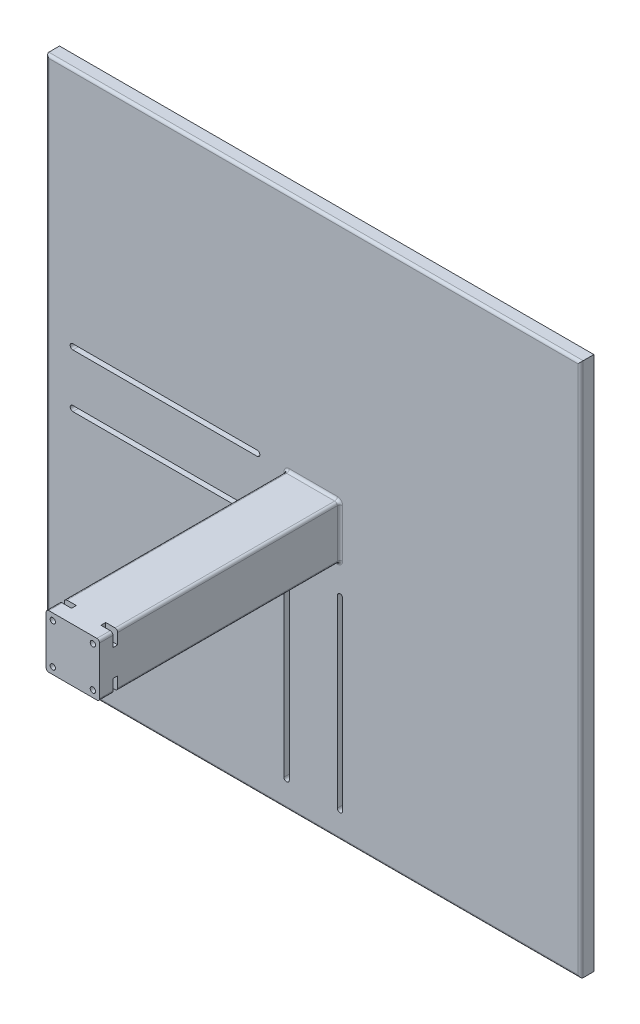
SolidWorks part; units mm, degrees
ref_plane "Plan de face" through (0, 0, 0) normal (0, 0, 1) x (1, 0, 0)
ref_plane "Plan de dessus" through (0, 0, 0) normal (0, 1, 0) x (1, 0, 0)
ref_plane "Plan de droite" through (0, 0, 0) normal (1, 0, 0) x (0, 0, -1)
sketch "Esquisse1" plane through (0, 0, 0) normal (0, 0, 1) x (1, 0, 0)
  line L1 (-100, 100) -> (100, 100)
  line L2 (-100, 100) -> (-100, -100)
  line L3 (-100, -100) -> (100, -100)
  line L4 (100, 100) -> (100, -100)
  dimension "D1" = 100
  dimension "D2" = 200
  dimension "D3" = 100
  dimension "D4" = 200
extrude "Boss.-Extru.1" add sketch "Esquisse1" along normal blind 5
sketch "Esquisse2" plane through (0, 0, 5) normal (0, 0, 1) x (1, 0, 0)
  line L0 (-100, 100) -> (-100, -100) construction
  line L1 (-15, -25) -> (15, -25)
  line L2 (-15, -25) -> (-15, -29)
  line L3 (-15, -29) -> (15, -29)
  line L4 (15, -25) -> (15, -29)
  line L5 (-25, 15) -> (-29, 15)
  line L6 (-25, 15) -> (-25, -15)
  line L7 (-25, -15) -> (-29, -15)
  line L8 (-29, 15) -> (-29, -15)
  line L9 (-100, -100) -> (100, -100) construction
  line L11 (100, -100) -> (100, 100) construction
  line L12 (100, 100) -> (-100, 100) construction
  point P12 (-25, 0)
  dimension "D1" = 75
  dimension "D2" = 75
  dimension "D3" = 30
  dimension "D4" = 30
  dimension "D5" = 85
  dimension "D6" = 85
  dimension "D7" = 85
  dimension "D8" = 85
  dimension "D9" = 4
  dimension "D10" = 4
extrude "Boss.-Extru.2" [suppressed] add sketch "Esquisse2" along normal blind 25
sketch "Esquisse3" [suppressed] plane through (0, 0, 5) normal (0, 0, 1) x (1, 0, 0)
  line L0 (-100, 100) -> (-100, -100) construction
  line L1 (-29, 20) -> (-100, 20)
  line L2 (-29, 20) -> (-29, -20)
  line L3 (-29, -20) -> (-100, -20)
  line L4 (-100, 20) -> (-100, -20)
  line L5 (-100, -100) -> (100, -100) construction
  line L6 (20, -100) -> (-20, -100)
  line L7 (20, -100) -> (20, -29)
  line L8 (20, -29) -> (-20, -29)
  line L9 (-20, -100) -> (-20, -29)
  line L10 (-15, -29) -> (15, -29) construction
  line L11 (-29, 15) -> (-29, -15) construction
  line L14 (-29, 15) -> (-29, -15) construction
  point P12 (0, -29)
  point P13 (-29, 0)
  dimension "D1" = 40
  dimension "D2" = 40
  dimension "D3" = 20
  dimension "D4" = 20
extrude "Boss.-Extru.3" [suppressed] add sketch "Esquisse3" along normal blind 5
fillet "Congé1" radius 1 4 edges at (0, -100, 5) (-100, 0, 5) (0, 100, 5) (100, 0, 5)
fillet "Congé2" [suppressed] radius 1
sketch "Esquisse4" plane through (0, 0, 5) normal (0, 0, 1) x (1, 0, 0)
  line L1 (-10, 10) -> (10, 10)
  line L2 (-10, 10) -> (-10, -10)
  line L3 (-10, -10) -> (10, -10)
  line L4 (10, 10) -> (10, -10)
  point P4 (0, 0)
  dimension "D1" = 10
  dimension "D2" = 20
  dimension "D3" = 10
  dimension "D4" = 20
extrude "Boss.-Extru.4" add sketch "Esquisse4" along normal blind 90
fillet "Congé3" radius 1 8 edges at (-10, 0, 5) (0, 10, 5) (0, -10, 5) (-10, 10, 50) (10, 10, 50) (10, 0, 5) (-10, -10, 50) (10, -10, 50)
sketch "Esquisse5" plane through (0, 0, 95) normal (0, 0, 1) x (1, 0, 0)
  line L0 (9, 10) -> (-9, 10) construction
  line L1 (-10, 9) -> (-10, -9) construction
  line L2 (10, -9) -> (10, 9) construction
  line L3 (-9, -10) -> (9, -10) construction
  circle A0 centre (7.5, 7.5) radius 1
  circle A1 centre (-7.5, 7.5) radius 1
  circle A2 centre (-7.5, -7.5) radius 1
  circle A3 centre (7.5, -7.5) radius 1
  dimension "D1" = 2
  dimension "D2" = 2.5
  dimension "D3" = 2.5
  dimension "D4" = 2.5
  dimension "D5" = 2.5
extrude "Enlèv. mat.-Extru.1" cut sketch "Esquisse5" against normal blind 5
sketch "Esquisse6" plane through (0, -10, 0) normal (0, -1, 0) x (1, 0, 0)
  line L0 (-9, 95) -> (9, 95) construction
  line L1 (-10, 90) -> (-5.5, 90)
  line L2 (-10, 90) -> (-10, 88.2)
  line L3 (-10, 88.2) -> (-5.5, 88.2)
  line L4 (-5.5, 90) -> (-5.5, 88.2)
  line L5 (10, 90) -> (5.5, 90)
  line L6 (10, 90) -> (10, 88.2)
  line L7 (10, 88.2) -> (5.5, 88.2)
  line L8 (5.5, 90) -> (5.5, 88.2)
  line L9 (-10, 6) -> (-10, 95) construction
  line L10 (10, 95) -> (10, 6) construction
  dimension "D2" = 5
  dimension "D3" = 1.8
  dimension "D5" = 4.5
  dimension "D6" = 4.5
extrude "Enlèv. mat.-Extru.2" cut sketch "Esquisse6" against normal blind 5
mirror "Symétrie1" about plane through (0, 0, 0) normal (0, 1, 0) of "Enlèv. mat.-Extru.2", "Enlèv. mat.-Extru.1"
sketch "Esquisse7" plane through (0, 0, 5) normal (0, 0, 1) x (1, 0, 0)
  line L0 (100, -100) -> (-100, -100) construction
  line L3 (10, -21) -> (10, -90) construction
  line L4 (11, -21) -> (11, -90)
  line L5 (9, -21) -> (9, -90)
  line L6 (-10, -21) -> (-10, -90) construction
  line L7 (-9, -21) -> (-9, -90)
  line L8 (-11, -21) -> (-11, -90)
  line L9 (-21, -10) -> (-90, -10) construction
  line L10 (-21, -11) -> (-90, -11)
  line L11 (-21, -9) -> (-90, -9)
  line L12 (-21, 10) -> (-90, 10) construction
  line L13 (-21, 9) -> (-90, 9)
  line L14 (-21, 11) -> (-90, 11)
  line L15 (9, -11) -> (-9, -11) construction
  line L16 (-100, -100) -> (-100, 100) construction
  line L17 (-11, -9) -> (-11, 9) construction
  arc A2 (11, -21) -> (9, -21) centre (10, -21) ccw
  arc A3 (9, -90) -> (11, -90) centre (10, -90) ccw
  arc A4 (-9, -21) -> (-11, -21) centre (-10, -21) ccw
  arc A5 (-11, -90) -> (-9, -90) centre (-10, -90) ccw
  arc A6 (-21, -11) -> (-21, -9) centre (-21, -10) ccw
  arc A7 (-90, -9) -> (-90, -11) centre (-90, -10) ccw
  arc A8 (-21, 9) -> (-21, 11) centre (-21, 10) ccw
  arc A9 (-90, 11) -> (-90, 9) centre (-90, 10) ccw
  point P6 (-11, 0)
  point P9 (10, -55.5)
  point P14 (-10, -55.5)
  point P21 (-55.5, -10)
  point P28 (-55.5, 10)
  point P37 (0, -11)
  dimension "D7" = 10
  dimension "D1" = 2
  dimension "D2" = 2
  dimension "D3" = 2
  dimension "D4" = 2
  dimension "D5" = 10
  dimension "D6" = 10
  dimension "D8" = 10
  dimension "D9" = 10
  dimension "D10" = 10
  dimension "D11" = 20
  dimension "D12" = 10
  dimension "D13" = 20
  dimension "D14" = 10
  dimension "D15" = 10
  dimension "D16" = 10
extrude "Enlèv. mat.-Extru.3" cut sketch "Esquisse7" against normal through all
